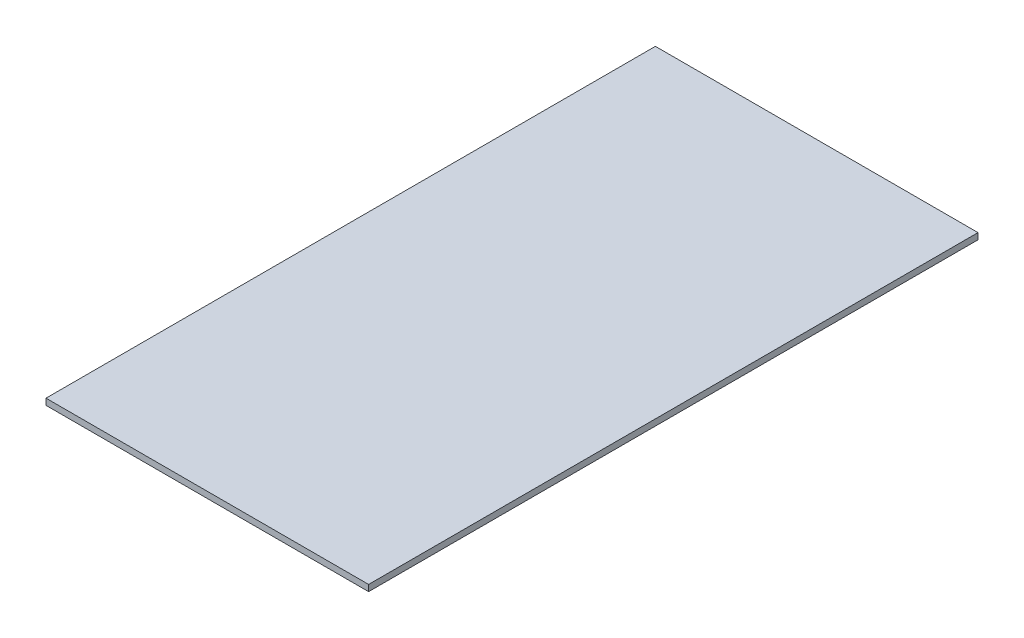
SolidWorks part; units mm, degrees
material "Silicon"
ref_plane "Front Plane" through (0, 0, 0) normal (0, 0, 1) x (1, 0, 0)
ref_plane "Top Plane" through (0, 0, 0) normal (0, 1, 0) x (1, 0, 0)
ref_plane "Right Plane" through (0, 0, 0) normal (1, 0, 0) x (0, 0, -1)
sketch "Sketch1" plane through (0, 0, 0) normal (0, 1, 0) x (1, 0, 0)
  line L1 (-35.5322, 109.623) -> (54.4678, 109.623)
  line L2 (-35.5322, 109.623) -> (-35.5322, -60.377)
  line L3 (-35.5322, -60.377) -> (54.4678, -60.377)
  line L4 (54.4678, 109.623) -> (54.4678, -60.377)
  dimension "D1" = 90
  dimension "D2" = 170
extrude "Boss-Extrude1" add sketch "Sketch1" along normal blind 1.75
sketch "Sketch2" plane through (0, 1.75, 0) normal (0, 1, 0) x (1, 0, 0)
  line L2 (9.4678, 109.623) -> (9.4678, -60.377) construction
  line L3 (-35.5322, 109.623) -> (54.4678, 109.623) construction
  line L4 (-35.5322, -60.377) -> (54.4678, -60.377) construction
  line L5 (-30.5322, 104.623) -> (49.4678, 104.623) construction
  line L6 (-35.5322, 109.623) -> (-35.5322, -60.377) construction
  line L7 (-35.5322, 24.623) -> (54.4678, 24.623) construction
  line L8 (54.4678, 109.623) -> (54.4678, -60.377) construction
  line L9 (49.4678, 104.623) -> (-30.5322, -55.377) construction
  circle A0 centre (-30.5322, 104.623) radius 1.6
  circle A1 centre (49.4678, 104.623) radius 1.6
  circle A2 centre (-30.5322, -55.377) radius 1.6
  circle A3 centre (49.4678, -55.377) radius 1.6
  point P14 (9.4678, 24.623)
  point P22 (9.4678, 24.623)
  dimension "D3" = 3.2
  dimension "D4" = 80
  dimension "D5" = 160
extrude "Cut-Extrude1" [suppressed] cut sketch "Sketch2" against normal blind 70.4
sketch "Sketch3" plane through (0, 1.75, 0) normal (0, 1, 0) x (1, 0, 0)
  line L0 (54.4678, -60.377) -> (54.4678, 109.623) construction
  line L1 (44.5378, -54.977) -> (28.5378, -54.977)
  line L2 (44.5378, -54.977) -> (44.5378, 4.023)
  line L3 (44.5378, 4.023) -> (28.5378, 4.023)
  line L4 (28.5378, -54.977) -> (28.5378, 4.023)
  line L5 (-35.5322, -60.377) -> (54.4678, -60.377) construction
  dimension "D1" = 25.93
  dimension "D2" = 16
  dimension "D3" = 59
  dimension "D4" = 5.4
extrude "Boss-Extrude2" [suppressed] add sketch "Sketch3" along normal blind 1
